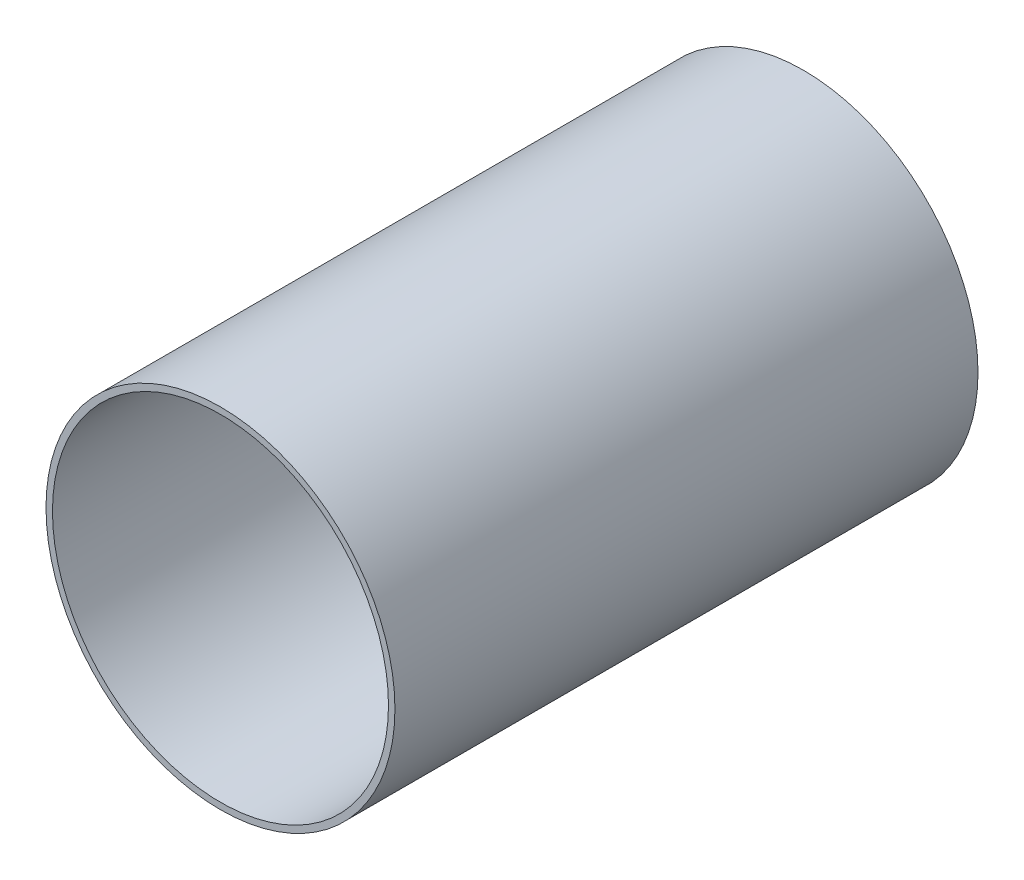
SolidWorks part; units mm, degrees
material "E-Glass Fiber"
ref_plane "Front Plane" through (0, 0, 0) normal (0, 0, 1) x (1, 0, 0)
ref_plane "Top Plane" through (0, 0, 0) normal (0, 1, 0) x (1, 0, 0)
ref_plane "Right Plane" through (0, 0, 0) normal (1, 0, 0) x (0, 0, -1)
sketch "Sketch1" plane through (0, 0, 0) normal (0, 0, 1) x (1, 0, 0)
  circle A0 centre (0, 0) radius 49.403
  circle A1 centre (0, 0) radius 47.5742
  dimension "D1" = 98.806
  dimension "D2" = 95.1484
extrude "Boss-Extrude1" add sketch "Sketch1" along normal blind 165.1
